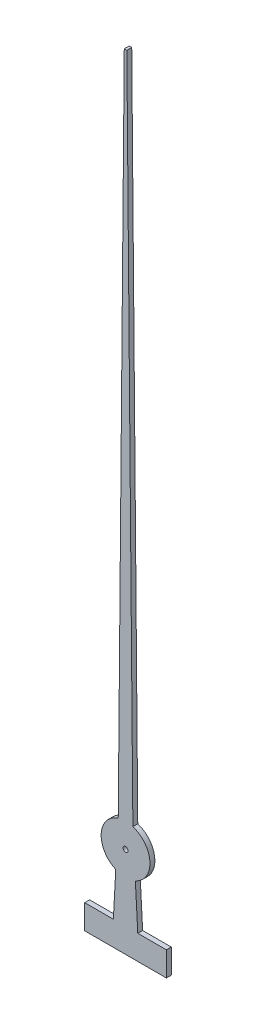
SolidWorks part; units mm, degrees
ref_plane "Front Plane" through (0, 0, 0) normal (0, 0, 1) x (1, 0, 0)
ref_plane "Top Plane" through (0, 0, 0) normal (0, 1, 0) x (1, 0, 0)
ref_plane "Right Plane" through (0, 0, 0) normal (1, 0, 0) x (0, 0, -1)
sketch "Sketch1" plane through (0, 0, 0) normal (0, 0, 1) x (1, 0, 0)
  line L0 (0, 16) -> (0, -1.3777) construction
  line L1 (0.2008, -0.4579) -> (0.25, -1.3643)
  line L2 (0.25, -1.3643) -> (0.8364, -1.3643)
  line L3 (0.8364, -1.3643) -> (0.8364, -1.8643)
  line L4 (0.15, 0.477) -> (0.0265, 14.1889)
  line L5 (-0.15, 0.477) -> (-0.0265, 14.1889)
  line L6 (-0.2008, -0.4579) -> (-0.25, -1.3643)
  line L7 (-0.8364, -1.8643) -> (0.8364, -1.8643)
  line L8 (-0.8364, -1.3643) -> (-0.8364, -1.8643)
  line L9 (-0.25, -1.3643) -> (-0.8364, -1.3643)
  line L10 (-0.0265, 14.1889) -> (0.0265, 14.1889)
  arc A0 (-0.15, 0.477) -> (-0.2008, -0.4579) centre (0, 0) ccw
  arc A1 (0.2008, -0.4579) -> (0.15, 0.477) centre (0, 0) ccw
  circle A2 centre (0, 0) radius 0.05
  dimension "D1" = 0.1
extrude "Boss-Extrude1" add sketch "Sketch1" along normal blind 0.1
